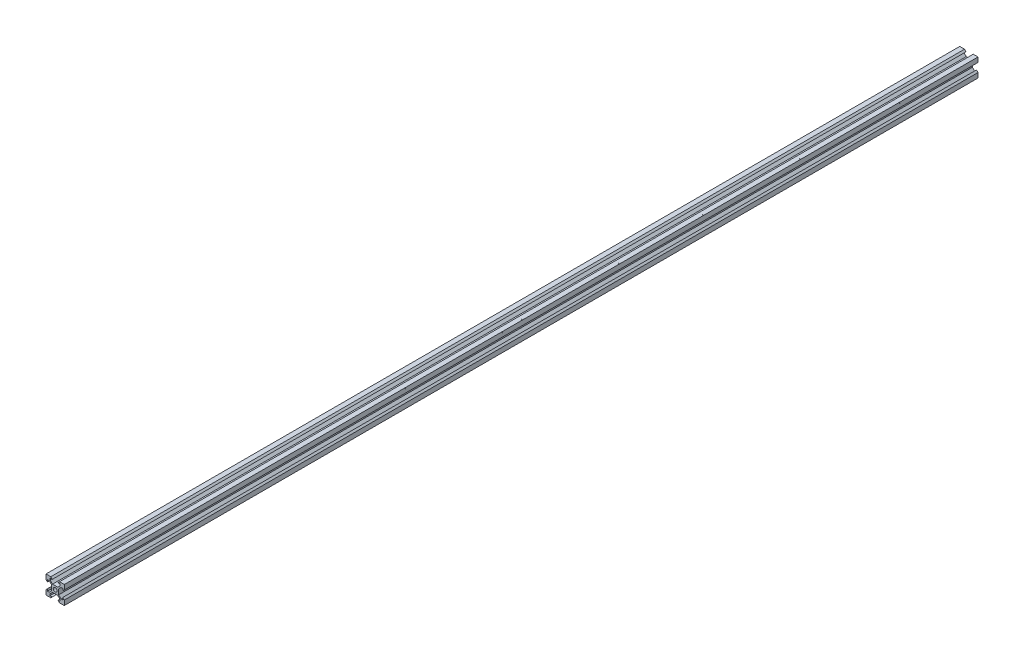
SolidWorks part; units mm, degrees
material "6061-T6 (SS)"
ref_plane "Front Plane" through (0, 0, 0) normal (0, 0, 1) x (1, 0, 0)
ref_plane "Top Plane" through (0, 0, 0) normal (0, 1, 0) x (1, 0, 0)
ref_plane "Right Plane" through (0, 0, 0) normal (1, 0, 0) x (0, 0, -1)
sketch "Sketch1" plane through (0, 0, 0) normal (0, 0, 1) x (1, 0, 0)
  line L0 (2.8343, 3.894) -> (5.5, 6.5588)
  line L1 (2.8343, -3.894) -> (-2.8343, -3.894)
  line L2 (3.8948, -2.8332) -> (3.8948, 2.8332)
  line L3 (2.8343, 3.894) -> (-2.8343, 3.894)
  line L4 (-3.8948, -2.8332) -> (-3.8948, 2.8332)
  line L5 (3.8994, -3.9006) -> (-3.8994, 3.9006) construction
  line L6 (3.9006, 3.8994) -> (-3.9006, -3.8994) construction
  line L7 (10, 4.747) -> (10, 9.9986)
  line L8 (5.5, 6.5588) -> (5.5, 8.3491)
  line L9 (5.5, 8.3491) -> (3.1, 8.3491)
  line L10 (3.1, 8.3491) -> (4.75, 9.9986)
  line L11 (4.75, 9.9986) -> (10, 9.9986)
  line L12 (8.35, 3.0975) -> (10, 4.747)
  line L13 (8.3507, 5.4975) -> (8.35, 3.0975)
  line L14 (6.5605, 5.498) -> (8.3507, 5.4975)
  line L15 (3.8948, 2.8332) -> (6.5605, 5.498)
  line L16 (0, -55) -> (0, 55) construction
  line L17 (-3.8948, 2.8332) -> (-6.5605, 5.498)
  line L18 (-6.5605, 5.498) -> (-8.3507, 5.4975)
  line L19 (-8.3507, 5.4975) -> (-8.35, 3.0975)
  line L20 (-8.35, 3.0975) -> (-10, 4.747)
  line L21 (-4.75, 9.9986) -> (-10, 9.9986)
  line L22 (-3.1, 8.3491) -> (-4.75, 9.9986)
  line L23 (-5.5, 8.3491) -> (-3.1, 8.3491)
  line L24 (-5.5, 6.5588) -> (-5.5, 8.3491)
  line L25 (-10, 4.747) -> (-10, 9.9986)
  line L26 (-2.8343, 3.894) -> (-5.5, 6.5588)
  line L27 (55, 0) -> (-55, 0) construction
  line L28 (3.8948, -2.8332) -> (6.5605, -5.498)
  line L29 (2.8343, -3.894) -> (5.5, -6.5588)
  line L30 (-3.8948, -2.8332) -> (-6.5605, -5.498)
  line L31 (-2.8343, -3.894) -> (-5.5, -6.5588)
  line L32 (-8.3507, -5.4975) -> (-8.35, -3.0975)
  line L33 (-8.35, -3.0975) -> (-10, -4.747)
  line L34 (8.3507, -5.4975) -> (8.35, -3.0975)
  line L35 (8.35, -3.0975) -> (10, -4.747)
  line L36 (-10, -4.747) -> (-10, -9.9986)
  line L37 (-5.5, -6.5588) -> (-5.5, -8.3491)
  line L38 (-5.5, -8.3491) -> (-3.1, -8.3491)
  line L39 (-3.1, -8.3491) -> (-4.75, -9.9986)
  line L40 (-4.75, -9.9986) -> (-10, -9.9986)
  line L41 (-6.5605, -5.498) -> (-8.3507, -5.4975)
  line L42 (6.5605, -5.498) -> (8.3507, -5.4975)
  line L43 (4.75, -9.9986) -> (10, -9.9986)
  line L44 (3.1, -8.3491) -> (4.75, -9.9986)
  line L45 (5.5, -8.3491) -> (3.1, -8.3491)
  line L46 (5.5, -6.5588) -> (5.5, -8.3491)
  line L47 (10, -4.747) -> (10, -9.9986)
  circle A0 centre (0, 0) radius 2.1
  point P0 (0, 0)
  dimension "D6" = 4.2
  dimension "D1" = 7.8
  dimension "D2" = 20
  dimension "D3" = 11
  dimension "D4" = 9.5
  dimension "D5" = 6.2
  dimension "D7" = 1.5
extrude "Boss-Extrude1" add sketch "Sketch1" along normal blind 1000
